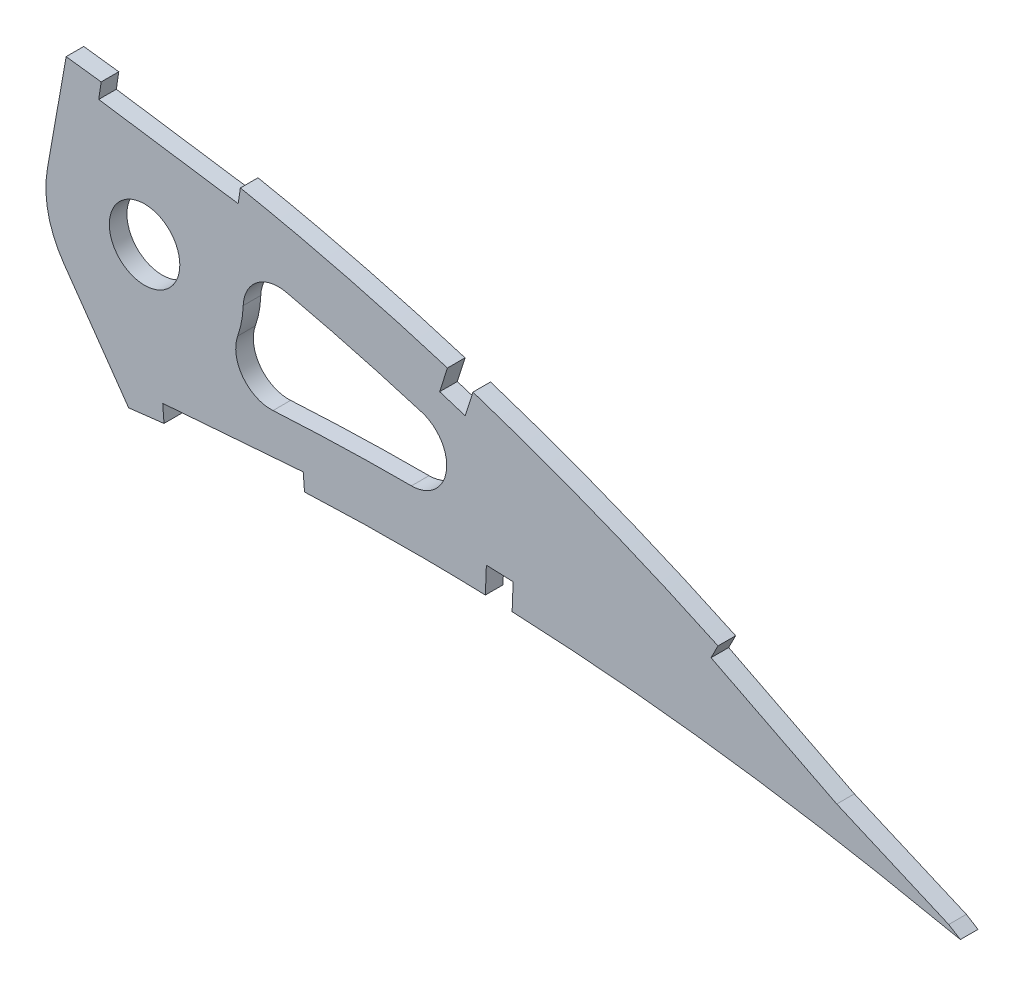
SolidWorks part; units mm, degrees
material "Pine"
ref_plane "Front Plane" through (0, 0, 0) normal (0, 0, 1) x (1, 0, 0)
ref_plane "Top Plane" through (0, 0, 0) normal (0, 1, 0) x (1, 0, 0)
ref_plane "Right Plane" through (0, 0, 0) normal (1, 0, 0) x (0, 0, -1)
curve "Curve2"
  spline degree 3 poles (520.229, 0.8111, 0) (520.1892, 0.8357, 0) (520.0299, 0.9341, 0) (519.6711, 1.1542, 0) (519.0735, 1.5208, 0) (518.237, 2.0313, 0) (517.1622, 2.6844, 0) (515.8486, 3.4756, 0) (514.2969, 4.4021, 0) (512.5075, 5.4598, 0) (510.4807, 6.6436, 0) (508.2172, 7.9486, 0) (505.7172, 9.3676, 0) (502.9816, 10.8948, 0) (500.0114, 12.5227, 0) (496.8072, 14.2443, 0) (493.3701, 16.0505, 0) (489.7015, 17.9338, 0) (485.8019, 19.8836, 0) (481.6733, 21.8919, 0) (477.317, 23.9487, 0) (472.7345, 26.0429, 0) (467.9284, 28.1661, 0) (462.9001, 30.305, 0) (457.6524, 32.4505, 0) (452.1876, 34.5902, 0) (446.5089, 36.7144, 0) (440.6184, 38.8094, 0) (434.5207, 40.866, 0) (428.2186, 42.8708, 0) (421.7166, 44.813, 0) (415.0186, 46.68, 0) (408.1302, 48.4622, 0) (401.0555, 50.1466, 0) (393.8008, 51.7219, 0) (386.3718, 53.1787, 0) (378.7746, 54.5024, 0) (371.0303, 55.692, 0) (363.2636, 56.6815, 0) (355.5128, 57.652, 0) (347.7736, 58.5637, 0) (339.9398, 59.4368, 0) (332.019, 60.2663, 0) (324.019, 61.0497, 0) (315.9478, 61.7836, 0) (307.814, 62.4658, 0) (299.6253, 63.0925, 0) (291.3904, 63.6628, 0) (283.1174, 64.1714, 0) (274.8152, 64.6183, 0) (266.4922, 65.0001, 0) (258.157, 65.3142, 0) (249.8185, 65.5589, 0) (241.4854, 65.7316, 0) (233.1666, 65.8314, 0) (224.8708, 65.8555, 0) (216.6071, 65.8035, 0) (208.384, 65.6736, 0) (200.2107, 65.464, 0) (192.0958, 65.1743, 0) (184.048, 64.8046, 0) (176.0762, 64.3519, 0) (168.189, 63.8191, 0) (160.3952, 63.2038, 0) (152.7034, 62.506, 0) (145.1216, 61.7286, 0) (137.6583, 60.8693, 0) (130.3214, 59.9308, 0) (123.1191, 58.9147, 0) (116.0593, 57.8206, 0) (109.1496, 56.6517, 0) (102.3976, 55.409, 0) (95.8102, 54.0963, 0) (89.3948, 52.714, 0) (83.1581, 51.266, 0) (77.1065, 49.7551, 0) (71.2467, 48.1838, 0) (65.5845, 46.5561, 0) (60.1256, 44.8756, 0) (54.8764, 43.1442, 0) (49.8409, 41.3683, 0) (45.0253, 39.5493, 0) (40.4333, 37.6928, 0) (36.0702, 35.8014, 0) (31.9393, 33.8806, 0) (28.0452, 31.9329, 0) (24.3908, 29.9636, 0) (20.9797, 27.9757, 0) (17.8153, 25.973, 0) (14.8987, 23.9604, 0) (12.2341, 21.9394, 0) (9.8224, 19.9149, 0) (7.6651, 17.8901, 0) (5.7652, 15.8664, 0) (4.1228, 13.8473, 0) (2.7399, 11.8344, 0) (1.6168, 9.8297, 0) (0.7561, 7.8345, 0) (0.1568, 5.85, 0) (-0.1712, 3.8792, 0) (-0.2528, 1.9205, 0) (-0.0842, 0.6392, 0) (0, 0, 0) knots 0 0 0 0 0.000254 0.001015 0.002283 0.004057 0.006331 0.009105 0.012374 0.016134 0.02038 0.025106 0.030306 0.035972 0.0421 0.048678 0.055702 0.06316 0.071046 0.07935 0.088063 0.097176 0.106678 0.116562 0.126814 0.137428 0.148394 0.1597 0.171338 0.183298 0.19557 0.208144 0.221012 0.234162 0.247587 0.261277 0.275223 0.289414 0.303771 0.317689 0.331784 0.34604 0.360444 0.374983 0.38964 0.404403 0.419257 0.434187 0.449177 0.464215 0.479284 0.49437 0.509458 0.524532 0.539579 0.554583 0.56953 0.584403 0.599191 0.613877 0.628447 0.642889 0.657186 0.671326 0.685294 0.699078 0.712665 0.726043 0.739198 0.752118 0.764792 0.777208 0.789356 0.801224 0.812804 0.824083 0.835055 0.84571 0.856038 0.866034 0.875689 0.884998 0.893953 0.902553 0.910789 0.918661 0.926166 0.933303 0.940071 0.946475 0.952518 0.958205 0.963547 0.968557 0.97325 0.977651 0.981787 0.985694 0.989415 0.993001 0.996508 1 1 1 1
curve "Curve3"
  spline degree 3 poles (0, 0, 0) (0.1336, -0.6306, 0) (0.4014, -1.8948, 0) (1.129, -3.7148, 0) (2.0912, -5.4642, 0) (3.3081, -7.1386, 0) (4.7718, -8.7374, 0) (6.479, -10.2623, 0) (8.428, -11.7125, 0) (10.6162, -13.0874, 0) (13.0406, -14.3883, 0) (15.6982, -15.6145, 0) (18.5868, -16.7656, 0) (21.7032, -17.8401, 0) (25.0435, -18.8396, 0) (28.6046, -19.7616, 0) (32.3825, -20.6074, 0) (36.3735, -21.375, 0) (40.5732, -22.065, 0) (44.9774, -22.6771, 0) (49.5814, -23.2117, 0) (54.3808, -23.6676, 0) (59.3708, -24.0458, 0) (64.5464, -24.3466, 0) (69.9027, -24.5709, 0) (75.4344, -24.718, 0) (81.1363, -24.7899, 0) (87.003, -24.788, 0) (93.0289, -24.7115, 0) (99.2088, -24.5648, 0) (105.5368, -24.3469, 0) (112.0073, -24.0604, 0) (118.6142, -23.7083, 0) (125.3518, -23.2917, 0) (132.2141, -22.8125, 0) (139.1951, -22.2745, 0) (146.2885, -21.679, 0) (153.4882, -21.0296, 0) (160.7876, -20.3295, 0) (168.1806, -19.5808, 0) (175.6606, -18.7872, 0) (183.2209, -17.9512, 0) (190.8551, -17.0772, 0) (198.5563, -16.1668, 0) (206.3179, -15.2253, 0) (214.1326, -14.2544, 0) (221.9939, -13.2579, 0) (229.8947, -12.2404, 0) (237.8276, -11.2019, 0) (245.786, -10.1497, 0) (253.7621, -9.0829, 0) (261.7491, -8.0072, 0) (269.7395, -6.9257, 0) (277.7256, -5.8389, 0) (285.7003, -4.7513, 0) (293.6562, -3.6657, 0) (301.5856, -2.5824, 0) (309.4812, -1.5067, 0) (317.3352, -0.4385, 0) (325.1402, 0.6201, 0) (332.8888, 1.6659, 0) (340.5737, 2.6975, 0) (348.187, 3.7144, 0) (355.721, 4.7168, 0) (363.0553, 5.6745, 0) (370.1707, 6.6383, 0) (377.0913, 7.4284, 0) (383.9258, 8.1028, 0) (390.6811, 8.6557, 0) (397.3493, 9.0951, 0) (403.9227, 9.4241, 0) (410.3934, 9.6473, 0) (416.7532, 9.7713, 0) (422.9943, 9.7993, 0) (429.1081, 9.7402, 0) (435.0867, 9.5987, 0) (440.9216, 9.3813, 0) (446.6049, 9.0952, 0) (452.1283, 8.7483, 0) (457.4837, 8.3456, 0) (462.6634, 7.8966, 0) (467.6597, 7.4078, 0) (472.4647, 6.8849, 0) (477.0715, 6.3387, 0) (481.4727, 5.7729, 0) (485.6616, 5.1968, 0) (489.6316, 4.6162, 0) (493.3764, 4.0385, 0) (496.89, 3.4693, 0) (500.1667, 2.916, 0) (503.2016, 2.384, 0) (505.9892, 1.8782, 0) (508.5257, 1.4052, 0) (510.8062, 0.9673, 0) (512.8275, 0.5717, 0) (514.5859, 0.2202, 0) (516.0789, -0.0824, 0) (517.3037, -0.3347, 0) (518.2586, -0.5328, 0) (518.9417, -0.6767, 0) (519.3522, -0.7624, 0) (519.5346, -0.8013, 0) (519.5802, -0.8111, 0) knots 0 0 0 0 0.003638 0.007293 0.011028 0.014901 0.018963 0.023258 0.027821 0.032679 0.037853 0.043362 0.049215 0.055422 0.061989 0.068918 0.076211 0.083868 0.091887 0.100266 0.109 0.118085 0.127515 0.137285 0.147388 0.157816 0.168563 0.179619 0.190977 0.202627 0.21456 0.226767 0.239236 0.251959 0.264924 0.27812 0.291536 0.30516 0.318981 0.332985 0.347163 0.361499 0.375981 0.390597 0.405333 0.420175 0.43511 0.450124 0.465203 0.480333 0.495501 0.51069 0.525887 0.541078 0.556247 0.571382 0.586466 0.601485 0.616424 0.631269 0.646007 0.660621 0.675098 0.689423 0.703582 0.716908 0.730009 0.742952 0.755726 0.76832 0.780724 0.792927 0.804916 0.816679 0.828204 0.839475 0.850481 0.861208 0.871639 0.881763 0.891564 0.901027 0.910139 0.918884 0.927249 0.935221 0.942785 0.949928 0.956638 0.962904 0.968712 0.974054 0.978918 0.983297 0.98718 0.990561 0.993433 0.995791 0.99763 0.998946 0.999737 1 1 1 1
sketch "Sketch1" plane through (0, 0, 0) normal (0, 0, 1) x (1, 0, 0)
  line L1 (502.7977, -0.7849) -> (507.4667, -1.7115)
  line L2 (503.4256, 0.7849) -> (507.4667, -1.7115)
  spline S2 degree 3 poles (0, 0) (0.1293, -0.6103) (0.3884, -1.8336) (1.0925, -3.5948) (2.0236, -5.2877) (3.2013, -6.908) (4.6177, -8.4552) (6.2698, -9.9309) (8.1558, -11.3342) (10.2733, -12.6647) (12.6193, -13.9236) (15.1912, -15.1102) (17.9865, -16.2241) (21.0022, -17.2639) (24.2346, -18.231) (27.6807, -19.1233) (31.3366, -19.9418) (35.1986, -20.6846) (39.2627, -21.3523) (43.5246, -21.9446) (47.9799, -22.4619) (52.6243, -22.9031) (57.4531, -23.2691) (62.4616, -23.5602) (67.6448, -23.7773) (72.9979, -23.9196) (78.5156, -23.9892) (84.1928, -23.9873) (90.0241, -23.9133) (96.0044, -23.7713) (102.128, -23.5605) (108.3894, -23.2833) (114.783, -22.9425) (121.303, -22.5394) (127.9436, -22.0756) (134.6991, -21.555) (141.5634, -20.9788) (148.5305, -20.3504) (155.5942, -19.6728) (162.7484, -18.9484) (169.9867, -18.1804) (177.3029, -17.3713) (184.6905, -16.5256) (192.1429, -15.6446) (199.6538, -14.7335) (207.2161, -13.794) (214.8235, -12.8296) (222.4691, -11.845) (230.1458, -10.84) (237.8471, -9.8218) (245.5656, -8.7896) (253.2946, -7.7486) (261.0269, -6.702) (268.755, -5.6503) (276.4722, -4.5978) (284.1711, -3.5473) (291.8444, -2.499) (299.485, -1.458) (307.0852, -0.4243) (314.6382, 0.6001) (322.1365, 1.6121) (329.5732, 2.6104) (336.9406, 3.5944) (344.2312, 4.5645) (351.3286, 5.4912) (358.2142, 6.4239) (364.9113, 7.1885) (371.525, 7.8411) (378.0621, 8.3761) (384.5149, 8.8013) (390.876, 9.1197) (397.1377, 9.3357) (403.2921, 9.4557) (409.3316, 9.4828) (415.2479, 9.4256) (421.0334, 9.2887) (426.6799, 9.0783) (432.1795, 8.8014) (437.5246, 8.4657) (442.7069, 8.076) (447.7194, 7.6415) (452.5543, 7.1686) (457.2041, 6.6625) (461.6621, 6.134) (465.9211, 5.5865) (469.9748, 5.029) (473.8165, 4.4671) (477.4403, 3.9081) (480.8404, 3.3572) (484.0114, 2.8219) (486.9482, 2.3069) (489.6458, 1.8176) (492.1004, 1.3598) (494.3072, 0.9361) (496.2632, 0.5532) (497.9648, 0.2131) (499.4095, -0.0797) (500.5948, -0.3239) (501.5189, -0.5155) (502.1799, -0.6549) (502.5771, -0.7378) (502.7536, -0.7754) (502.7977, -0.7849) knots 0 0 0 0 0.003638 0.007293 0.011028 0.014901 0.018963 0.023258 0.027821 0.032679 0.037853 0.043362 0.049215 0.055422 0.061989 0.068918 0.076211 0.083868 0.091887 0.100266 0.109 0.118085 0.127515 0.137285 0.147388 0.157816 0.168563 0.179619 0.190977 0.202627 0.21456 0.226767 0.239236 0.251959 0.264924 0.27812 0.291536 0.30516 0.318981 0.332985 0.347163 0.361499 0.375981 0.390597 0.405333 0.420175 0.43511 0.450124 0.465203 0.480333 0.495501 0.51069 0.525887 0.541078 0.556247 0.571382 0.586466 0.601485 0.616424 0.631269 0.646007 0.660621 0.675098 0.689423 0.703582 0.716908 0.730009 0.742952 0.755726 0.76832 0.780724 0.792927 0.804916 0.816679 0.828204 0.839475 0.850481 0.861208 0.871639 0.881763 0.891564 0.901027 0.910139 0.918884 0.927249 0.935221 0.942785 0.949928 0.956638 0.962904 0.968712 0.974054 0.978918 0.983297 0.98718 0.990561 0.993433 0.995791 0.99763 0.998946 0.999737 1 1 1 1
  spline S3 degree 3 poles (503.4256, 0.7849) (503.3871, 0.8087) (503.2329, 0.9039) (502.8857, 1.1169) (502.3075, 1.4716) (501.498, 1.9657) (500.4579, 2.5977) (499.1867, 3.3633) (497.6851, 4.26) (495.9535, 5.2834) (493.9922, 6.429) (491.8018, 7.6919) (489.3825, 9.0651) (486.7353, 10.5429) (483.8611, 12.1183) (480.7604, 13.7842) (477.4343, 15.5321) (473.8841, 17.3545) (470.1105, 19.2413) (466.1153, 21.1848) (461.8997, 23.1751) (457.4652, 25.2017) (452.8143, 27.2563) (447.9484, 29.3262) (442.8702, 31.4023) (437.5819, 33.4729) (432.0866, 35.5285) (426.3865, 37.5558) (420.4857, 39.546) (414.3871, 41.4861) (408.0952, 43.3656) (401.6135, 45.1723) (394.9475, 46.8969) (388.1015, 48.5268) (381.0811, 50.0513) (373.8919, 51.461) (366.5401, 52.742) (359.046, 53.8931) (351.5302, 54.8507) (344.0298, 55.7898) (336.5405, 56.6721) (328.9598, 57.517) (321.2948, 58.3197) (313.5531, 59.0778) (305.7427, 59.788) (297.8716, 60.4482) (289.9474, 61.0547) (281.9785, 61.6064) (273.9728, 62.0987) (265.9387, 62.5311) (257.8845, 62.9006) (249.8186, 63.2046) (241.7494, 63.4413) (233.6854, 63.6085) (225.6353, 63.7051) (217.6075, 63.7284) (209.6107, 63.678) (201.6532, 63.5523) (193.7439, 63.3495) (185.8911, 63.0691) (178.1033, 62.7114) (170.3889, 62.2734) (162.7565, 61.7577) (155.2145, 61.1624) (147.7711, 60.4871) (140.4342, 59.7347) (133.2119, 58.9033) (126.1121, 57.995) (119.1423, 57.0118) (112.3106, 55.953) (105.6241, 54.8218) (99.0901, 53.6193) (92.7156, 52.349) (86.5074, 51.0113) (80.4721, 49.6101) (74.616, 48.148) (68.9454, 46.6275) (63.4661, 45.0524) (58.1835, 43.4261) (53.1039, 41.7506) (48.2311, 40.0321) (43.571, 38.2719) (39.1273, 36.4754) (34.9051, 34.645) (30.9076, 32.7863) (27.1393, 30.9015) (23.603, 28.9958) (20.3021, 27.0721) (17.2398, 25.134) (14.4175, 23.1865) (11.839, 21.2308) (9.5051, 19.2717) (7.4175, 17.3123) (5.579, 15.3539) (3.9896, 13.4) (2.6514, 11.4522) (1.5646, 9.5122) (0.7317, 7.5814) (0.1518, 5.6611) (-0.1657, 3.7539) (-0.2447, 1.8584) (-0.0814, 0.6186) (0, 0) knots 0 0 0 0 0.000254 0.001015 0.002283 0.004057 0.006331 0.009105 0.012374 0.016134 0.02038 0.025106 0.030306 0.035972 0.0421 0.048678 0.055702 0.06316 0.071046 0.07935 0.088063 0.097176 0.106678 0.116562 0.126814 0.137428 0.148394 0.1597 0.171338 0.183298 0.19557 0.208144 0.221012 0.234162 0.247587 0.261277 0.275223 0.289414 0.303771 0.317689 0.331784 0.34604 0.360444 0.374983 0.38964 0.404403 0.419257 0.434187 0.449177 0.464215 0.479284 0.49437 0.509458 0.524532 0.539579 0.554583 0.56953 0.584403 0.599191 0.613877 0.628447 0.642889 0.657186 0.671326 0.685294 0.699078 0.712665 0.726043 0.739198 0.752118 0.764792 0.777208 0.789356 0.801224 0.812804 0.824083 0.835055 0.84571 0.856038 0.866034 0.875689 0.884998 0.893953 0.902553 0.910789 0.918661 0.926166 0.933303 0.940071 0.946475 0.952518 0.958205 0.963547 0.968557 0.97325 0.977651 0.981787 0.985694 0.989415 0.993001 0.996508 1 1 1 1
extrude "Boss-Extrude1" add sketch "Sketch1" along normal blind 3.175
sketch "Sketch4" plane through (0, 0, 3.175) normal (0, 0, 1) x (1, 0, 0)
  line L0 (342.9777, 36.32) -> (346.3588, 55.4952)
  line L1 (345.923, 23.0344) -> (357.6226, 6.3256)
  line L2 (360.4876, 33.2326) -> (390.7312, 33.2326)
  circle A0 centre (360.4876, 33.2326) radius 17.78
  circle A1 centre (360.4876, 33.2326) radius 6.35
  spline S0 degree 3 poles (-1939.359, -486.1193) (49.033, 56.5957) (-7.3857, 17.6121) (1.0925, -3.5948) (2.0236, -5.2877) (3.2013, -6.908) (4.6177, -8.4552) (6.2698, -9.9309) (8.1558, -11.3342) (10.2733, -12.6647) (12.6193, -13.9236) (15.1912, -15.1102) (17.9865, -16.2241) (21.0022, -17.2639) (24.2346, -18.231) (27.6807, -19.1233) (31.3366, -19.9418) (35.1986, -20.6846) (39.2627, -21.3523) (43.5246, -21.9446) (47.9799, -22.4619) (52.6243, -22.9031) (57.4531, -23.2691) (62.4616, -23.5602) (67.6448, -23.7773) (72.9979, -23.9196) (78.5156, -23.9892) (84.1928, -23.9873) (90.0241, -23.9133) (96.0044, -23.7713) (102.128, -23.5605) (108.3894, -23.2833) (114.783, -22.9425) (121.303, -22.5394) (127.9436, -22.0756) (134.6991, -21.555) (141.5634, -20.9788) (148.5305, -20.3504) (155.5942, -19.6728) (162.7484, -18.9484) (169.9867, -18.1804) (177.3029, -17.3713) (184.6905, -16.5256) (192.1429, -15.6446) (199.6538, -14.7335) (207.2161, -13.794) (214.8235, -12.8296) (222.4691, -11.845) (230.1458, -10.84) (237.8471, -9.8218) (245.5656, -8.7896) (253.2946, -7.7486) (261.0269, -6.702) (268.755, -5.6503) (276.4722, -4.5978) (284.1711, -3.5473) (291.8444, -2.499) (299.485, -1.458) (307.0852, -0.4243) (314.6382, 0.6001) (322.1365, 1.6121) (329.5732, 2.6104) (336.9406, 3.5944) (344.2312, 4.5645) (351.3286, 5.4912) (358.2142, 6.4239) (364.9113, 7.1885) (371.525, 7.8411) (378.0621, 8.3761) (384.5149, 8.8013) (390.876, 9.1197) (397.1377, 9.3357) (403.2921, 9.4557) (409.3316, 9.4828) (415.2479, 9.4256) (421.0334, 9.2887) (426.6799, 9.0783) (432.1795, 8.8014) (437.5246, 8.4657) (442.7069, 8.076) (447.7194, 7.6415) (452.5543, 7.1686) (457.2041, 6.6625) (461.6621, 6.134) (465.9211, 5.5865) (469.9748, 5.029) (473.8165, 4.4671) (477.4403, 3.9081) (480.8404, 3.3572) (484.0114, 2.8219) (486.9482, 2.3069) (489.6458, 1.8176) (492.1004, 1.3598) (494.3072, 0.9361) (496.2632, 0.5532) (497.9648, 0.2131) (499.4095, -0.0797) (500.5948, -0.3239) (501.5189, -0.5155) (502.1799, -0.6549) (517.7197, -3.8983) (531.8047, -12.9312) (961.8177, 1945.365) knots -0.121768 -0.121768 -0.121768 -0.121768 0.003638 0.007293 0.011028 0.014901 0.018963 0.023258 0.027821 0.032679 0.037853 0.043362 0.049215 0.055422 0.061989 0.068918 0.076211 0.083868 0.091887 0.100266 0.109 0.118085 0.127515 0.137285 0.147388 0.157816 0.168563 0.179619 0.190977 0.202627 0.21456 0.226767 0.239236 0.251959 0.264924 0.27812 0.291536 0.30516 0.318981 0.332985 0.347163 0.361499 0.375981 0.390597 0.405333 0.420175 0.43511 0.450124 0.465203 0.480333 0.495501 0.51069 0.525887 0.541078 0.556247 0.571382 0.586466 0.601485 0.616424 0.631269 0.646007 0.660621 0.675098 0.689423 0.703582 0.716908 0.730009 0.742952 0.755726 0.76832 0.780724 0.792927 0.804916 0.816679 0.828204 0.839475 0.850481 0.861208 0.871639 0.881763 0.891564 0.901027 0.910139 0.918884 0.927249 0.935221 0.942785 0.949928 0.956638 0.962904 0.968712 0.974054 0.978918 0.983297 0.98718 0.990561 0.993433 0.995791 0.99763 0.998946 0.999737 1.090356 1.090356 1.090356 1.090356 only from (0, 0) to (502.7977, -0.7849) construction
  spline S1 degree 3 poles (1596.0847, 1675.4542) (530.0817, -21.8378) (517.9824, -8.1433) (502.8857, 1.1169) (502.3075, 1.4716) (501.498, 1.9657) (500.4579, 2.5977) (499.1867, 3.3633) (497.6851, 4.26) (495.9535, 5.2834) (493.9922, 6.429) (491.8018, 7.6919) (489.3825, 9.0651) (486.7353, 10.5429) (483.8611, 12.1183) (480.7604, 13.7842) (477.4343, 15.5321) (473.8841, 17.3545) (470.1105, 19.2413) (466.1153, 21.1848) (461.8997, 23.1751) (457.4652, 25.2017) (452.8143, 27.2563) (447.9484, 29.3262) (442.8702, 31.4023) (437.5819, 33.4729) (432.0866, 35.5285) (426.3865, 37.5558) (420.4857, 39.546) (414.3871, 41.4861) (408.0952, 43.3656) (401.6135, 45.1723) (394.9475, 46.8969) (388.1015, 48.5268) (381.0811, 50.0513) (373.8919, 51.461) (366.5401, 52.742) (359.046, 53.8931) (351.5302, 54.8507) (344.0298, 55.7898) (336.5405, 56.6721) (328.9598, 57.517) (321.2948, 58.3197) (313.5531, 59.0778) (305.7427, 59.788) (297.8716, 60.4482) (289.9474, 61.0547) (281.9785, 61.6064) (273.9728, 62.0987) (265.9387, 62.5311) (257.8845, 62.9006) (249.8186, 63.2046) (241.7494, 63.4413) (233.6854, 63.6085) (225.6353, 63.7051) (217.6075, 63.7284) (209.6107, 63.678) (201.6532, 63.5523) (193.7439, 63.3495) (185.8911, 63.0691) (178.1033, 62.7114) (170.3889, 62.2734) (162.7565, 61.7577) (155.2145, 61.1624) (147.7711, 60.4871) (140.4342, 59.7347) (133.2119, 58.9033) (126.1121, 57.995) (119.1423, 57.0118) (112.3106, 55.953) (105.6241, 54.8218) (99.0901, 53.6193) (92.7156, 52.349) (86.5074, 51.0113) (80.4721, 49.6101) (74.616, 48.148) (68.9454, 46.6275) (63.4661, 45.0524) (58.1835, 43.4261) (53.1039, 41.7506) (48.2311, 40.0321) (43.571, 38.2719) (39.1273, 36.4754) (34.9051, 34.645) (30.9076, 32.7863) (27.1393, 30.9015) (23.603, 28.9958) (20.3021, 27.0721) (17.2398, 25.134) (14.4175, 23.1865) (11.839, 21.2308) (9.5051, 19.2717) (7.4175, 17.3123) (5.579, 15.3539) (3.9896, 13.4) (2.6514, 11.4522) (1.5646, 9.5122) (0.7317, 7.5814) (0.1518, 5.6611) (-0.1657, 3.7539) (-1.1153, -19.0274) (65.1985, -36.9717) (-1990.693, -186.6939) knots -0.096988 -0.096988 -0.096988 -0.096988 0.000254 0.001015 0.002283 0.004057 0.006331 0.009105 0.012374 0.016134 0.02038 0.025106 0.030306 0.035972 0.0421 0.048678 0.055702 0.06316 0.071046 0.07935 0.088063 0.097176 0.106678 0.116562 0.126814 0.137428 0.148394 0.1597 0.171338 0.183298 0.19557 0.208144 0.221012 0.234162 0.247587 0.261277 0.275223 0.289414 0.303771 0.317689 0.331784 0.34604 0.360444 0.374983 0.38964 0.404403 0.419257 0.434187 0.449177 0.464215 0.479284 0.49437 0.509458 0.524532 0.539579 0.554583 0.56953 0.584403 0.599191 0.613877 0.628447 0.642889 0.657186 0.671326 0.685294 0.699078 0.712665 0.726043 0.739198 0.752118 0.764792 0.777208 0.789356 0.801224 0.812804 0.824083 0.835055 0.84571 0.856038 0.866034 0.875689 0.884998 0.893953 0.902553 0.910789 0.918661 0.926166 0.933303 0.940071 0.946475 0.952518 0.958205 0.963547 0.968557 0.97325 0.977651 0.981787 0.985694 0.989415 0.993001 0.996508 1.116632 1.116632 1.116632 1.116632 only from (503.4256, 0.7849) to (0, 0) construction
  spline S2 degree 3 poles (0, 0) (0.1293, -0.6103) (0.3884, -1.8336) (1.0925, -3.5948) (2.0236, -5.2877) (3.2013, -6.908) (4.6177, -8.4552) (6.2698, -9.9309) (8.1558, -11.3342) (10.2733, -12.6647) (12.6193, -13.9236) (15.1912, -15.1102) (17.9865, -16.2241) (21.0022, -17.2639) (24.2346, -18.231) (27.6807, -19.1233) (31.3366, -19.9418) (35.1986, -20.6846) (39.2627, -21.3523) (43.5246, -21.9446) (47.9799, -22.4619) (52.6243, -22.9031) (57.4531, -23.2691) (62.4616, -23.5602) (67.6448, -23.7773) (72.9979, -23.9196) (78.5156, -23.9892) (84.1928, -23.9873) (90.0241, -23.9133) (96.0044, -23.7713) (102.128, -23.5605) (108.3894, -23.2833) (114.783, -22.9425) (121.303, -22.5394) (127.9436, -22.0756) (134.6991, -21.555) (141.5634, -20.9788) (148.5305, -20.3504) (155.5942, -19.6728) (162.7484, -18.9484) (169.9867, -18.1804) (177.3029, -17.3713) (184.6905, -16.5256) (192.1429, -15.6446) (199.6538, -14.7335) (207.2161, -13.794) (214.8235, -12.8296) (222.4691, -11.845) (230.1458, -10.84) (237.8471, -9.8218) (245.5656, -8.7896) (253.2946, -7.7486) (261.0269, -6.702) (268.755, -5.6503) (276.4722, -4.5978) (284.1711, -3.5473) (291.8444, -2.499) (299.485, -1.458) (307.0852, -0.4243) (314.6382, 0.6001) (322.1365, 1.6121) (329.5732, 2.6104) (336.9406, 3.5944) (344.2312, 4.5645) (351.3286, 5.4912) (358.2142, 6.4239) (364.9113, 7.1885) (371.525, 7.8411) (378.0621, 8.3761) (384.5149, 8.8013) (390.876, 9.1197) (397.1377, 9.3357) (403.2921, 9.4557) (409.3316, 9.4828) (415.2479, 9.4256) (421.0334, 9.2887) (426.6799, 9.0783) (432.1795, 8.8014) (437.5246, 8.4657) (442.7069, 8.076) (447.7194, 7.6415) (452.5543, 7.1686) (457.2041, 6.6625) (461.6621, 6.134) (465.9211, 5.5865) (469.9748, 5.029) (473.8165, 4.4671) (477.4403, 3.9081) (480.8404, 3.3572) (484.0114, 2.8219) (486.9482, 2.3069) (489.6458, 1.8176) (492.1004, 1.3598) (494.3072, 0.9361) (496.2632, 0.5532) (497.9648, 0.2131) (499.4095, -0.0797) (500.5948, -0.3239) (501.5189, -0.5155) (502.1799, -0.6549) (502.5771, -0.7378) (502.7536, -0.7754) (502.7977, -0.7849) knots 0 0 0 0 0.003638 0.007293 0.011028 0.014901 0.018963 0.023258 0.027821 0.032679 0.037853 0.043362 0.049215 0.055422 0.061989 0.068918 0.076211 0.083868 0.091887 0.100266 0.109 0.118085 0.127515 0.137285 0.147388 0.157816 0.168563 0.179619 0.190977 0.202627 0.21456 0.226767 0.239236 0.251959 0.264924 0.27812 0.291536 0.30516 0.318981 0.332985 0.347163 0.361499 0.375981 0.390597 0.405333 0.420175 0.43511 0.450124 0.465203 0.480333 0.495501 0.51069 0.525887 0.541078 0.556247 0.571382 0.586466 0.601485 0.616424 0.631269 0.646007 0.660621 0.675098 0.689423 0.703582 0.716908 0.730009 0.742952 0.755726 0.76832 0.780724 0.792927 0.804916 0.816679 0.828204 0.839475 0.850481 0.861208 0.871639 0.881763 0.891564 0.901027 0.910139 0.918884 0.927249 0.935221 0.942785 0.949928 0.956638 0.962904 0.968712 0.974054 0.978918 0.983297 0.98718 0.990561 0.993433 0.995791 0.99763 0.998946 0.999737 1 1 1 1
  spline S3 degree 3 poles (503.4256, 0.7849) (503.3871, 0.8087) (503.2329, 0.9039) (502.8857, 1.1169) (502.3075, 1.4716) (501.498, 1.9657) (500.4579, 2.5977) (499.1867, 3.3633) (497.6851, 4.26) (495.9535, 5.2834) (493.9922, 6.429) (491.8018, 7.6919) (489.3825, 9.0651) (486.7353, 10.5429) (483.8611, 12.1183) (480.7604, 13.7842) (477.4343, 15.5321) (473.8841, 17.3545) (470.1105, 19.2413) (466.1153, 21.1848) (461.8997, 23.1751) (457.4652, 25.2017) (452.8143, 27.2563) (447.9484, 29.3262) (442.8702, 31.4023) (437.5819, 33.4729) (432.0866, 35.5285) (426.3865, 37.5558) (420.4857, 39.546) (414.3871, 41.4861) (408.0952, 43.3656) (401.6135, 45.1723) (394.9475, 46.8969) (388.1015, 48.5268) (381.0811, 50.0513) (373.8919, 51.461) (366.5401, 52.742) (359.046, 53.8931) (351.5302, 54.8507) (344.0298, 55.7898) (336.5405, 56.6721) (328.9598, 57.517) (321.2948, 58.3197) (313.5531, 59.0778) (305.7427, 59.788) (297.8716, 60.4482) (289.9474, 61.0547) (281.9785, 61.6064) (273.9728, 62.0987) (265.9387, 62.5311) (257.8845, 62.9006) (249.8186, 63.2046) (241.7494, 63.4413) (233.6854, 63.6085) (225.6353, 63.7051) (217.6075, 63.7284) (209.6107, 63.678) (201.6532, 63.5523) (193.7439, 63.3495) (185.8911, 63.0691) (178.1033, 62.7114) (170.3889, 62.2734) (162.7565, 61.7577) (155.2145, 61.1624) (147.7711, 60.4871) (140.4342, 59.7347) (133.2119, 58.9033) (126.1121, 57.995) (119.1423, 57.0118) (112.3106, 55.953) (105.6241, 54.8218) (99.0901, 53.6193) (92.7156, 52.349) (86.5074, 51.0113) (80.4721, 49.6101) (74.616, 48.148) (68.9454, 46.6275) (63.4661, 45.0524) (58.1835, 43.4261) (53.1039, 41.7506) (48.2311, 40.0321) (43.571, 38.2719) (39.1273, 36.4754) (34.9051, 34.645) (30.9076, 32.7863) (27.1393, 30.9015) (23.603, 28.9958) (20.3021, 27.0721) (17.2398, 25.134) (14.4175, 23.1865) (11.839, 21.2308) (9.5051, 19.2717) (7.4175, 17.3123) (5.579, 15.3539) (3.9896, 13.4) (2.6514, 11.4522) (1.5646, 9.5122) (0.7317, 7.5814) (0.1518, 5.6611) (-0.1657, 3.7539) (-0.2447, 1.8584) (-0.0814, 0.6186) (0, 0) knots 0 0 0 0 0.000254 0.001015 0.002283 0.004057 0.006331 0.009105 0.012374 0.016134 0.02038 0.025106 0.030306 0.035972 0.0421 0.048678 0.055702 0.06316 0.071046 0.07935 0.088063 0.097176 0.106678 0.116562 0.126814 0.137428 0.148394 0.1597 0.171338 0.183298 0.19557 0.208144 0.221012 0.234162 0.247587 0.261277 0.275223 0.289414 0.303771 0.317689 0.331784 0.34604 0.360444 0.374983 0.38964 0.404403 0.419257 0.434187 0.449177 0.464215 0.479284 0.49437 0.509458 0.524532 0.539579 0.554583 0.56953 0.584403 0.599191 0.613877 0.628447 0.642889 0.657186 0.671326 0.685294 0.699078 0.712665 0.726043 0.739198 0.752118 0.764792 0.777208 0.789356 0.801224 0.812804 0.824083 0.835055 0.84571 0.856038 0.866034 0.875689 0.884998 0.893953 0.902553 0.910789 0.918661 0.926166 0.933303 0.940071 0.946475 0.952518 0.958205 0.963547 0.968557 0.97325 0.977651 0.981787 0.985694 0.989415 0.993001 0.996508 1 1 1 1
  spline S4 degree 1 poles (498.0859, -7.8588) (10.022, 1.7185) knots 0 0 1 1 construction
  spline S5 degree 1 poles (10.022, 1.7185) (504.9173, 9.1516) knots 0 0 1 1 construction
  spline S6 degree 3 poles (498.0859, -7.8588) (497.9469, -7.7729) (497.6755, -7.6063) (497.0745, -7.2376) (496.073, -6.6257) (494.034, -5.3896) (489.9509, -2.9592) (481.7087, 1.7828) (464.948, 10.7477) (440.2507, 22.0083) (414.6791, 31.031) (393.8046, 36.8155) (380.602, 39.8235) (369.9822, 41.8499) (361.9478, 43.1977) (353.9876, 44.3116) (345.6865, 45.3455) (337.4905, 46.3384) (326.5045, 47.5759) (307.2867, 49.5386) (279.7715, 51.732) (246.7179, 53.3195) (213.6646, 53.7552) (180.6691, 52.9014) (147.8152, 50.5632) (120.6625, 47.1646) (99.1877, 43.3787) (83.2589, 39.9382) (67.5746, 35.8064) (54.8041, 31.6869) (44.8785, 27.8959) (37.6273, 24.7728) (30.6423, 21.3346) (24.0439, 17.5382) (18.0447, 13.3493) (13.8923, 9.5446) (11.5209, 6.5233) (10.5748, 4.8197) (10.1543, 3.6588) (10.0297, 3.1195) (9.9672, 2.6225) (9.9572, 2.3998) (9.9588, 2.3191) (9.9601, 2.2824) (9.9755, 2.1081) (9.998, 1.9117) (10.0142, 1.7801) (10.022, 1.7185) knots 0 0 0 0 0.000976 0.001952 0.003903 0.007806 0.015612 0.031224 0.062448 0.124896 0.187344 0.218568 0.249792 0.265404 0.281016 0.296629 0.312241 0.327853 0.343465 0.374689 0.437137 0.499585 0.562033 0.624481 0.686929 0.749377 0.780601 0.811825 0.843049 0.874274 0.889886 0.905498 0.92111 0.936722 0.952334 0.967946 0.975752 0.983558 0.987461 0.991364 0.993315 0.995267 0.996242 0.997218 0.998194 0.998682 0.99917 0.99917 0.99917 0.99917
  spline S7 degree 3 poles (10.022, 1.7185) (10.0347, 1.6599) (10.0621, 1.5353) (10.1053, 1.3469) (10.1485, 1.1764) (10.1634, 1.1269) (10.1846, 1.0623) (10.2582, 0.8739) (10.471, 0.4378) (10.7582, -0.0307) (11.4745, -0.9405) (12.8348, -2.2117) (15.8465, -4.2506) (20.7309, -6.5276) (27.4244, -8.6509) (34.5678, -10.2856) (41.9694, -11.5214) (49.5311, -12.4386) (59.7521, -13.3077) (72.7026, -13.8464) (88.3798, -13.8504) (104.1321, -13.363) (125.1917, -12.1985) (151.5744, -9.9789) (183.2656, -6.5394) (214.9809, -2.61) (246.7126, 1.5971) (278.4754, 5.9283) (304.9613, 9.5471) (323.5218, 12.0515) (334.1258, 13.4688) (340.757, 14.3528) (346.0757, 15.0514) (350.0239, 15.5708) (353.9954, 16.1055) (358.0945, 16.6309) (362.1894, 17.1023) (367.6256, 17.6763) (377.1849, 18.5459) (390.8533, 19.3786) (412.7664, 19.8538) (440.1321, 18.8575) (467.3149, 15.8619) (486.1639, 12.8099) (495.5577, 11.0534) (499.8832, 10.1925) (501.9026, 9.7801) (502.8845, 9.5777) (503.7571, 9.3959) (504.3754, 9.2659) (504.7415, 9.1891) (504.9173, 9.1516) knots 0.000865 0.000865 0.000865 0.000865 0.001353 0.00184 0.002816 0.003792 0.004768 0.006719 0.008671 0.012573 0.016476 0.024282 0.032088 0.047699 0.063311 0.078922 0.094534 0.110145 0.125757 0.15698 0.188203 0.219426 0.250649 0.313095 0.37554 0.437986 0.500432 0.562878 0.625324 0.656547 0.672159 0.68777 0.695576 0.703382 0.711187 0.718993 0.726799 0.734605 0.750216 0.781439 0.812662 0.875108 0.937554 0.968777 0.984389 0.992194 0.994146 0.996097 0.998049 0.999024 1 1 1 1
  dimension "D1" = 35.56
  dimension "D3" = 80
  dimension "D4" = 55
  dimension "D2" = 10.16
extrude "Cut-Extrude2" cut sketch "Sketch4" against normal blind 7.62
sketch "Sketch5" plane through (0, 0, 3.175) normal (0, 0, 1) x (1, 0, 0)
  line L1 (352.6921, 54.8905) -> (352.2294, 51.7498)
  line L3 (377.8179, 51.1893) -> (352.6921, 54.8905)
  line L5 (415.1161, 41.459) -> (413.6569, 36.8603)
  line L7 (422.066, 14.0099) -> (421.8846, 9.1885)
  line L9 (426.8874, 13.8284) -> (422.066, 14.0099)
  line L11 (419.7148, 39.9998) -> (415.1161, 41.459)
  line L13 (463.9822, 22.6301) -> (462.5448, 19.7991)
  line L15 (486.5411, 11.1759) -> (463.9822, 22.6301)
  line L17 (509.7692, 1.1434) -> (486.5411, 11.1759)
  line L19 (389.0717, 12.0535) -> (363.7545, 10.0956)
  line L21 (363.7545, 10.0956) -> (363.9992, 6.9309)
  line L23 (363.9992, 6.9309) -> (389.3165, 8.8889)
  line L25 (389.3165, 8.8889) -> (389.0717, 12.0535)
  line L27 (352.2294, 51.7498) -> (377.3553, 48.0485)
  line L29 (377.3553, 48.0485) -> (377.8179, 51.1893)
  line L31 (421.8846, 9.1885) -> (426.706, 9.007)
  line L33 (426.706, 9.007) -> (426.8874, 13.8284)
  line L35 (413.6569, 36.8603) -> (418.2556, 35.4011)
  line L37 (418.2556, 35.4011) -> (419.7148, 39.9998)
  line L39 (462.5448, 19.7991) -> (485.1923, 8.3)
  line L41 (485.1923, 8.3) -> (508.5102, -1.7713)
  line L43 (508.5102, -1.7713) -> (509.7692, 1.1434)
extrude "Cut-Extrude3" cut sketch "Sketch5" against normal blind 7.62
fillet "Fillet1" radius 6.35 3 edges at (449.31, 17.6882, 1.5875) (369.3635, 17.8265, 1.5875) (376.692, 40.55, 1.5875)
